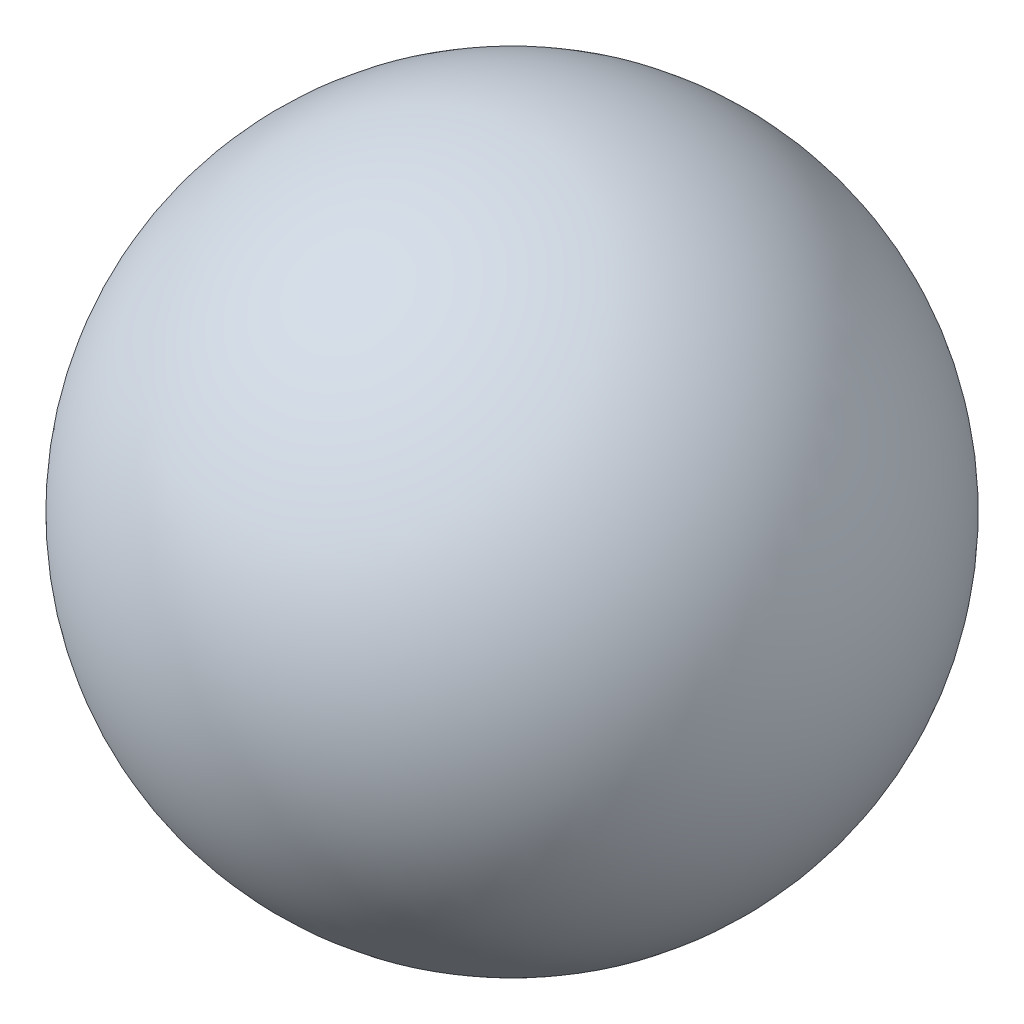
SolidWorks part; units mm, degrees
ref_plane "Plan de face" through (0, 0, 0) normal (0, 0, 1) x (1, 0, 0)
ref_plane "Plan de dessus" through (0, 0, 0) normal (0, 1, 0) x (1, 0, 0)
ref_plane "Plan de droite" through (0, 0, 0) normal (1, 0, 0) x (0, 0, -1)
sketch "Esquisse1" plane through (0, 0, 0) normal (0, 0, 1) x (1, 0, 0)
  line L0 (0, 7.5) -> (0, -7.5)
  arc A0 (0, 7.5) -> (0, -7.5) centre (0, 0) ccw
  dimension "D1" = 7.5
revolve "Révolution1" add sketch "Esquisse1" angle 360 about L0
